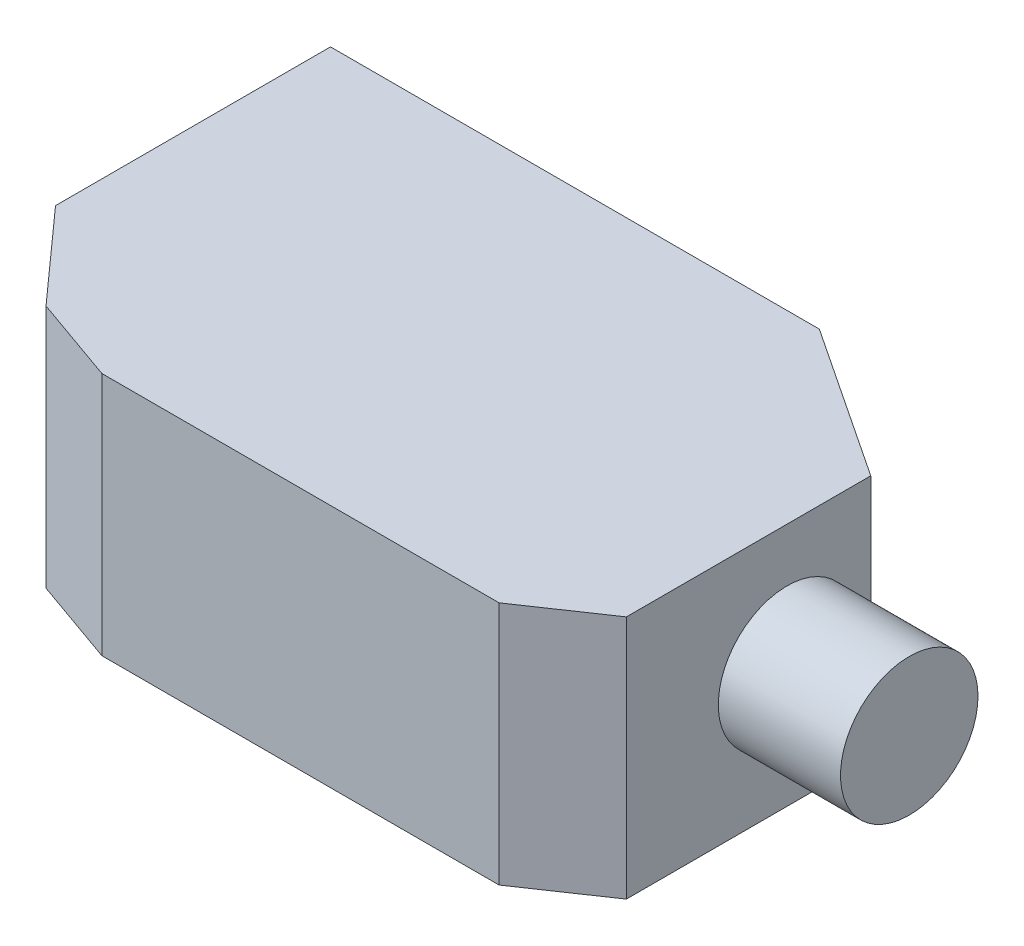
SolidWorks part; units mm, degrees
ref_plane "Front Plane" through (0, 0, 0) normal (0, 0, 1) x (1, 0, 0)
ref_plane "Top Plane" through (0, 0, 0) normal (0, 1, 0) x (1, 0, 0)
ref_plane "Right Plane" through (0, 0, 0) normal (1, 0, 0) x (0, 0, -1)
sketch "Sketch1" plane through (0, 0, 0) normal (0, 1, 0) x (1, 0, 0)
  line L0 (0, 0) -> (25.4, 0)
  line L1 (25.4, 0) -> (33.3375, -5.2651)
  line L2 (33.3375, -5.2651) -> (33.3375, -17.9651)
  line L3 (33.3375, -17.9651) -> (29.3954, -20.6375)
  line L4 (29.3954, -20.6375) -> (8.7579, -20.6375)
  line L5 (8.7579, -20.6375) -> (4.2678, -19.05)
  line L6 (0, 0) -> (0, -14.2875)
  line L7 (0, -14.2875) -> (4.2678, -19.05)
  dimension "D1" = 25.4
  dimension "D2" = 9.525
  dimension "D3" = 12.7
  dimension "D4" = 4.7625
  dimension "D5" = 20.6375
  dimension "D6" = 4.7625
  dimension "D7" = 14.2875
  dimension "D8" = 33.3375
  dimension "D9" = 20.6375
  dimension "D10" = 19.05
extrude "Boss-Extrude1" add sketch "Sketch1" along normal blind 12.7
sketch "Sketch2" plane through (33.3375, 0, 0) normal (1, 0, 0) x (0, 0, -1)
  line L1 (-17.9651, 12.7) -> (-5.2651, 12.7) construction
  line L3 (-5.2651, 12.7) -> (-5.2651, 0) construction
  circle A0 centre (-9.6149, 6.35) radius 3.5719
  dimension "D1" = 7.1437
  dimension "D2" = 6.35
  dimension "D3" = 4.3498
extrude "Boss-Extrude2" add sketch "Sketch2" along normal blind 6.35
